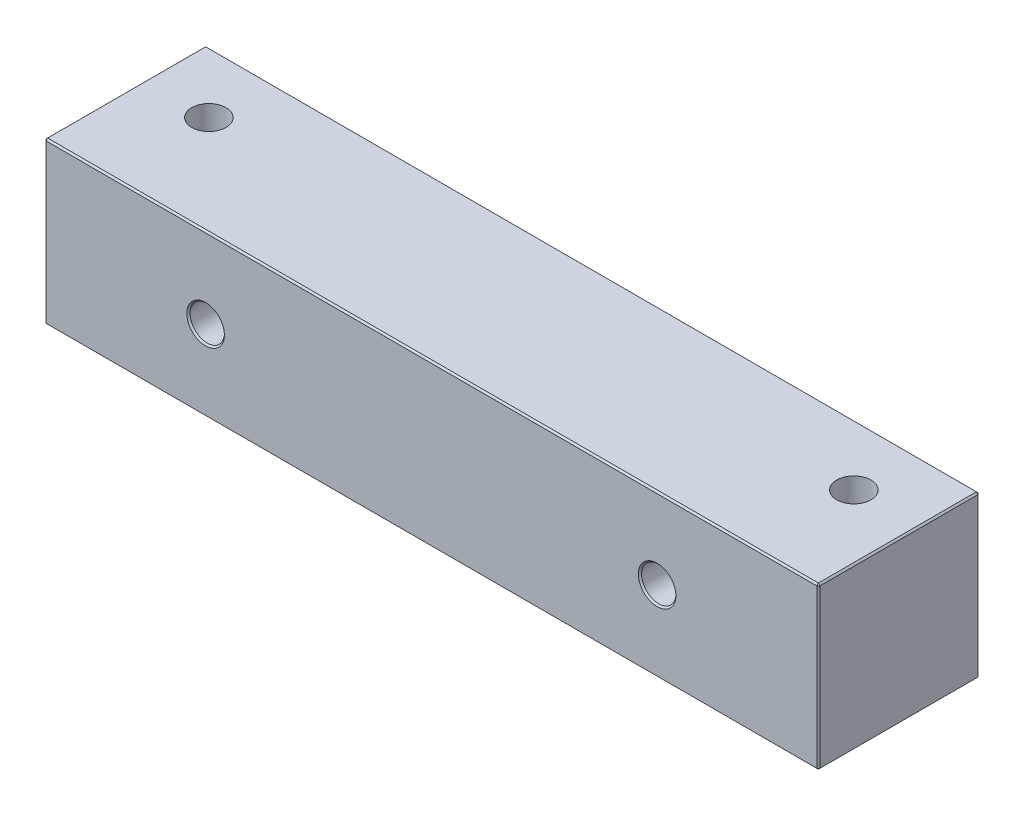
SolidWorks part; units mm, degrees
material "6063-T6"
ref_plane "Front" through (0, 0, 0) normal (0, 0, 1) x (1, 0, 0)
ref_plane "Top" through (0, 0, 0) normal (0, 1, 0) x (1, 0, 0)
ref_plane "Right" through (0, 0, 0) normal (1, 0, 0) x (0, 0, -1)
sketch "Sketch1" plane through (0, 0, 0) normal (0, 1, 0) x (1, 0, 0)
  line L1 (-30.48, 6.35) -> (30.48, 6.35)
  line L2 (-30.48, 6.35) -> (-30.48, -6.35)
  line L3 (-30.48, -6.35) -> (30.48, -6.35)
  line L4 (30.48, 6.35) -> (30.48, -6.35)
  line L5 (-30.48, 6.35) -> (30.48, -6.35) construction
  line L6 (-30.48, -6.35) -> (30.48, 6.35) construction
  point P0 (0, 0)
  dimension "D1" = 12.7
  dimension "D2" = 60.96
extrude "Boss-Extrude1" add sketch "Sketch1" along normal mid plane 12.7
hole_wizard "#6-32 Tapped Hole1" positions "Sketch2" profile "Sketch3" tap size "#6-32" standard "ANSI Inch" end condition through all
sketch "Sketch2" plane through (0, 6.35, 0) normal (0, 1, 0) x (1, 0, 0)
  line L0 (30.48, 6.35) -> (-30.48, 6.35) construction
  point P0 (-25.4, 1.524)
  point P2 (25.4, 1.524)
  point P6 (0, 6.35)
  dimension "D1" = 50.8
  dimension "D2" = 25.4
  dimension "D3" = 4.826
cosmetic thread "Hole Thread1" parameters "D1"=7.0104, "D2"=3.5052
cosmetic thread "Hole Thread2" parameters "D1"=7.0104, "D2"=3.5052
sketch "Sketch3" plane through (-25.4, 6.35, -1.524) normal (1, 0, 0) x (0, 0, 1)
  line L0 (0, 0) -> (0, 12.7)
  line L1 (0, 12.7) -> (1.3525, 12.7)
  line L2 (1.3525, 12.7) -> (1.3525, 0)
  line L5 (1.3525, 0) -> (0, 0)
  line L11 (0, -6.35) -> (0, 107.95) construction
  dimension "Thru Tap Drill Dia." = 2.7051
  dimension "Thru Tap Drill Depth" = 12.7
hole_wizard "#6-32 Tapped Hole2" positions "Sketch4" profile "Sketch5" tap size "#6-32" standard "ANSI Inch" end condition through all
sketch "Sketch4" plane through (0, 0, 6.35) normal (0, 0, 1) x (1, 0, 0)
  line L0 (-30.48, 6.35) -> (30.48, 6.35) construction
  point P0 (-17.78, 0)
  point P2 (17.78, 0)
  point P6 (0, 6.35)
  dimension "D1" = 35.56
  dimension "D2" = 6.35
  dimension "D3" = 17.78
sketch "Sketch5" plane through (-17.78, 0, 6.35) normal (1, 0, 0) x (0, -1, 0)
  line L0 (0, 0) -> (0, 12.7)
  line L1 (0, 12.7) -> (1.3525, 12.7)
  line L2 (1.3525, 12.7) -> (1.3525, 0)
  line L5 (1.3525, 0) -> (0, 0)
  line L11 (0, -6.35) -> (0, 107.95) construction
  dimension "Thru Tap Drill Dia." = 2.7051
  dimension "Thru Tap Drill Depth" = 12.7
cosmetic thread "Hole Thread3" parameters "D1"=7.0104, "D2"=3.5052
cosmetic thread "Hole Thread4" parameters "D1"=7.0104, "D2"=3.5052
chamfer "Chamfer1" distance 0.127 angle 45 16 edges at (19.1325, 0, -6.35) (-16.4275, 0, -6.35) (30.48, 6.35, 0) (30.48, -6.35, 0) (-30.48, 6.35, 0) (30.48, 0, -6.35) (0, 6.35, -6.35) (-30.48, 0, -6.35) (0, -6.35, -6.35) (-30.48, -6.35, 0) (-30.48, 0, 6.35) (0, 6.35, 6.35) (30.48, 0, 6.35) (0, -6.35, 6.35) (19.1325, 0, 6.35) (-16.4275, 0, 6.35)
